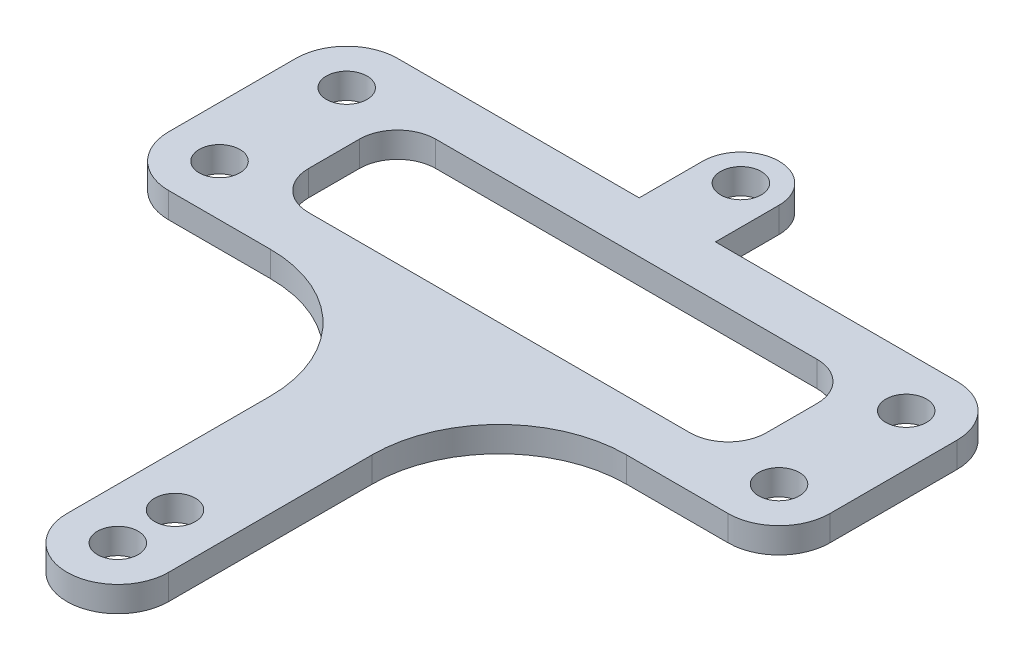
SolidWorks part; units mm, degrees
ref_plane "Front Plane" through (0, 0, 0) normal (0, 0, 1) x (1, 0, 0)
ref_plane "Top Plane" through (0, 0, 0) normal (0, 1, 0) x (1, 0, 0)
ref_plane "Right Plane" through (0, 0, 0) normal (1, 0, 0) x (0, 0, -1)
sketch "Sketch1" plane through (0, 0, 0) normal (0, 1, 0) x (1, 0, 0)
  line L2 (26, -5) -> (26, -15)
  line L3 (4, 0) -> (4, -1)
  line L4 (22, -1) -> (4, -1)
  line L5 (-4, -1) -> (-4, 0)
  line L7 (22, -19) -> (4, -19)
  line L8 (4, -30) -> (4, -19)
  line L9 (-4, -30) -> (-4, -19)
  line L10 (-22, -1) -> (-4, -1)
  line L11 (-4, 0) -> (-4, -1)
  line L12 (-26, -5) -> (-26, -15)
  line L13 (-4, -45) -> (-4, -30)
  line L14 (-22, -19) -> (-4, -19)
  line L15 (4, -1) -> (4, 0)
  line L16 (4, -45) -> (4, -30)
  line L17 (-1.6, -30) -> (-1.6, -45)
  line L19 (1.6, -30) -> (1.6, -45)
  circle A0 centre (0, 0) radius 1.6
  arc A1 (4, 0) -> (-4, 0) centre (0, 0) ccw
  circle A2 centre (22, -5) radius 1.6
  arc A3 (26, -5) -> (22, -1) centre (22, -5) ccw
  circle A4 centre (22, -15) radius 1.6
  arc A5 (22, -19) -> (26, -15) centre (22, -15) ccw
  arc A6 (1.6, -30) -> (-1.6, -30) centre (0, -30) ccw
  arc A8 (-22, -19) -> (-26, -15) centre (-22, -15) cw
  circle A9 centre (-22, -15) radius 1.6
  arc A10 (-26, -5) -> (-22, -1) centre (-22, -5) cw
  circle A11 centre (-22, -5) radius 1.6
  arc A12 (-4, -45) -> (4, -45) centre (0, -45) ccw
  arc A13 (-1.6, -45) -> (1.6, -45) centre (0, -45) ccw
extrude "Boss-Extrude1" add sketch "Sketch1" along normal blind 2 contours L13 A12 L16 L8 L7 A5 L2 A3 L4 L3 A1 L5 L10 A10 L12 A8 L14 L9 A13 L17 A6 L19 A11 A0 A2 A4 A9
fillet "Fillet1" radius 10 2 edges at (-4, 1, 19) (4, 1, 19)
sketch "Sketch2" plane through (0, 2, 0) normal (0, 1, 0) x (1, 0, 0)
  line L0 (0, 0) -> (0, 3)
  line L1 (-4, 0) -> (-4, 3)
  line L2 (4, 0) -> (4, 3)
  circle A0 centre (0, 3) radius 4
  circle A1 centre (0, 0) radius 4
  circle A2 centre (0, 3) radius 1.6
extrude "Boss-Extrude3" add sketch "Sketch2" against normal up to surface (2 mm away)
sketch "Sketch4" plane through (0, 2, 0) normal (0, 1, 0) x (1, 0, 0)
  circle A0 centre (0, 3) radius 1.6
extrude "Cut-Extrude2" cut sketch "Sketch4" against normal blind 4
sketch "Sketch5" plane through (0, 2, 0) normal (0, 1, 0) x (1, 0, 0)
  line L0 (-4, -1) -> (4, -1)
  line L1 (-4, -1) -> (-11.9576, 14.4075)
  line L2 (-11.9576, 14.4075) -> (9.1218, 12.8952)
  line L3 (9.1218, 12.8952) -> (4, -1)
extrude "Cut-Extrude3" cut sketch "Sketch5" against normal blind 10
sketch "Sketch6" plane through (0, 2, 0) normal (0, 1, 0) x (1, 0, 0)
  line L0 (22, -1) -> (-22, -1) construction
  circle A0 centre (0, -1) radius 3
  circle A1 centre (0, -1) radius 1.6
extrude "Boss-Extrude4" add sketch "Sketch6" against normal up to surface (2 mm away) up to face at (0, 0, 37.5)
sketch "Sketch7" plane through (0, 2, 0) normal (0, 1, 0) x (1, 0, 0)
  line L0 (1.6, -1) -> (-1.6, -1) construction
  circle A0 centre (0, -1) radius 1.6
extrude "Cut-Extrude4" cut sketch "Sketch7" against normal blind 10
sketch "Sketch8" plane through (0, 2, 0) normal (0, 1, 0) x (1, 0, 0)
  line L0 (-18, -5) -> (-18, -15)
  line L1 (18, -5) -> (18, -15)
  line L2 (18, -15) -> (-18, -15)
  line L3 (-18, -5) -> (18, -5)
  circle A0 centre (-22, -5) radius 4
  circle A1 centre (-22, -15) radius 4
  circle A2 centre (22, -15) radius 4
  circle A3 centre (22, -5) radius 4
extrude "Cut-Extrude6" cut sketch "Sketch8" against normal blind 9.5 contours L3 L0 L2 L1
fillet "Fillet3" radius 3 4 edges at (18, 1, 5) (18, 1, 15) (-18, 1, 15) (-18, 1, 5)
sketch "Sketch9" plane through (0, 2, 0) normal (0, 1, 0) x (1, 0, 0)
  circle A0 centre (0, -1) radius 1.6
extrude "Boss-Extrude5" add sketch "Sketch9" against normal up to surface (2 mm away) up to face at (0, 0, 16.5536)
sketch "Sketch10" plane through (0, 2, 0) normal (0, 1, 0) x (1, 0, 0)
  line L0 (3, -1) -> (3, 3)
  line L1 (3, -1) -> (-3, -1)
  line L2 (-3, -1) -> (-3, 3)
  arc A0 (3, 3) -> (-3, 3) centre (0, 3) ccw
  circle A1 centre (0, 3) radius 1.6
extrude "Boss-Extrude6" add sketch "Sketch10" against normal up to surface (2 mm away) up to face at (0, 0, 16.5536)
sketch "Sketch11" plane through (0, 2, 0) normal (0, 1, 0) x (1, 0, 0)
  circle A0 centre (0, 3) radius 1.6
extrude "Cut-Extrude7" cut sketch "Sketch11" against normal blind 10
sketch "Sketch12" plane through (0, 2, 0) normal (0, 1, 0) x (1, 0, 0)
  line L1 (-3, 3) -> (-3, 4)
  line L3 (3, 4) -> (3, 3)
  line L4 (3, 3) -> (2.8284, 3)
  line L5 (-2.8284, 3) -> (-3, 3)
  arc A0 (-2.8284, 3) -> (2.8284, 3) centre (0, 4) ccw
  arc A1 (3, 4) -> (-3, 4) centre (0, 4) ccw
extrude "Boss-Extrude7" add sketch "Sketch12" against normal up to surface (2 mm away) up to face at (0, 0, 14.381)
sketch "Sketch13" plane through (0, 2, 0) normal (0, 1, 0) x (1, 0, 0)
  circle A0 centre (0, 4) radius 1.6
extrude "Cut-Extrude9" cut sketch "Sketch13" against normal blind 5.5
sketch "Sketch14" plane through (0, 2, 0) normal (0, 1, 0) x (1, 0, 0)
sketch "Sketch15" plane through (0, 2, 0) normal (0, 1, 0) x (1, 0, 0)
  line L0 (-4, -45) -> (-4, -23.9538)
  line L1 (-4, -23.9538) -> (4, -23.9538)
  line L2 (4, -23.9538) -> (4, -45)
  arc A1 (-4, -45) -> (4, -45) centre (0, -45) ccw
extrude "Boss-Extrude8" add sketch "Sketch15" against normal up to surface (2 mm away) up to face at (0, 0, -2.4)
sketch "Sketch16" plane through (0, 2, 0) normal (0, 1, 0) x (1, 0, 0)
  circle A0 centre (0, -45) radius 1.6
  circle A1 centre (0, -36) radius 1.6
extrude "Cut-Extrude10" cut sketch "Sketch16" against normal blind 10
sketch "Sketch17" plane through (0, 2, 0) normal (0, 1, 0) x (1, 0, 0)
  circle A0 centre (0, -36) radius 2.8849
extrude "Boss-Extrude9" add sketch "Sketch17" against normal blind 1
sketch "Sketch18" plane through (0, 1, 0) normal (0, -1, 0) x (-1, 0, 0)
  circle A0 centre (0, -36) radius 1.6
extrude "Boss-Extrude10" add sketch "Sketch18" along normal blind 3
sketch "Sketch19" plane through (0, -2, 0) normal (0, -1, 0) x (-1, 0, 0)
  circle A0 centre (0, -36) radius 1.6
  circle A1 centre (0, -36) radius 1.5
extrude "Cut-Extrude11" cut sketch "Sketch19" against normal up to surface (2 mm away) up to face at (0, 0, 46.6)
sketch "Sketch20" plane through (0, 0, 0) normal (0, -1, 0) x (-1, 0, 0)
  circle A0 centre (0, -40.5) radius 1.6
extrude "Cut-Extrude12" cut sketch "Sketch20" against normal blind 10
sketch "Sketch21" plane through (0, 0, 0) normal (0, -1, 0) x (-1, 0, 0)
  circle A1 centre (0, -36) radius 1.5
extrude "Cut-Extrude13" cut sketch "Sketch21" along normal blind 8.5
